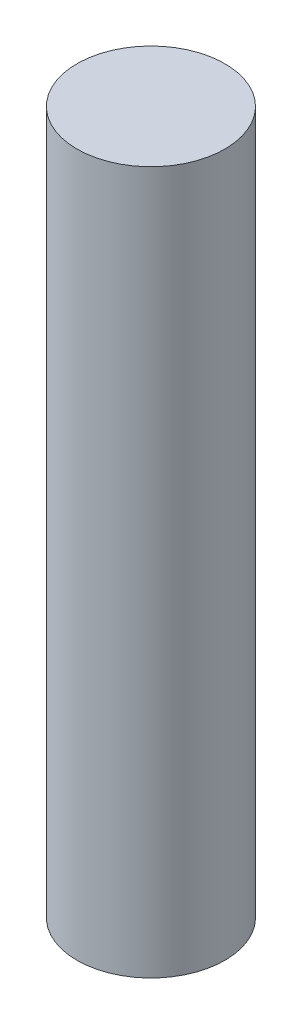
SolidWorks part; units mm, degrees
ref_plane "Front Plane" through (0, 0, 0) normal (0, 0, 1) x (1, 0, 0)
ref_plane "Top Plane" through (0, 0, 0) normal (0, 1, 0) x (1, 0, 0)
ref_plane "Right Plane" through (0, 0, 0) normal (1, 0, 0) x (0, 0, -1)
sketch "Sketch1" plane through (0, 0, 0) normal (0, 1, 0) x (1, 0, 0)
  circle A0 centre (0, 0) radius 1
  dimension "D1" = 2
extrude "Boss-Extrude1" add sketch "Sketch1" along normal blind 9.5
ref_plane "Plane1" through (0, 4.75, 0) normal (0, -1, 0) x (-1, 0, 0)
